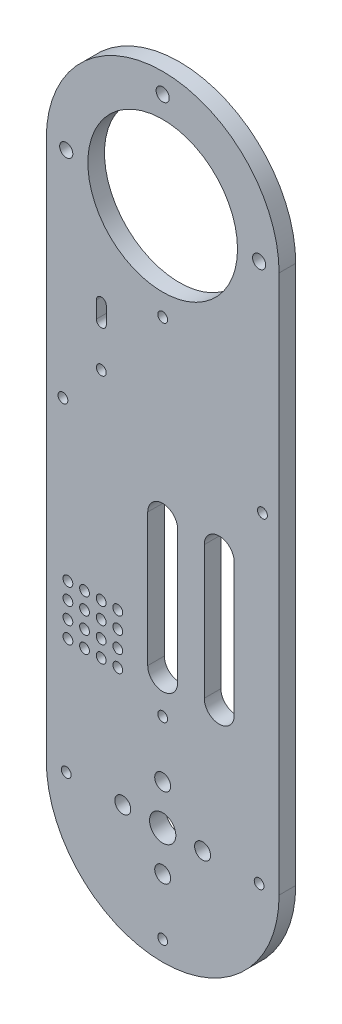
SolidWorks part; units mm, degrees
ref_plane "Front Plane" through (0, 0, 0) normal (0, 0, 1) x (1, 0, 0)
ref_plane "Top Plane" through (0, 0, 0) normal (0, 1, 0) x (1, 0, 0)
ref_plane "Right Plane" through (0, 0, 0) normal (1, 0, 0) x (0, 0, -1)
sketch "Sketch1" plane through (0, 0, 0) normal (0, 0, 1) x (1, 0, 0)
  line L0 (35, 0) -> (35, 162)
  line L1 (-35, 0) -> (-35, 162)
  line L2 (-35, 162) -> (35, 162) construction
  line L3 (0, 0) -> (35, 0) construction
  line L4 (0, 0) -> (0, 40) construction
  line L5 (0, 0) -> (25.0676, 25.0676) construction
  line L6 (0, 0) -> (0, 162) construction
  line L7 (0, 80) -> (0, 40) construction
  line L8 (4.5, 80) -> (4.5, 40)
  line L9 (-4.5, 80) -> (-4.5, 40)
  line L10 (0, 162) -> (0, 191) construction
  line L13 (17, 80) -> (17, 40) construction
  line L14 (21.5, 80) -> (21.5, 40)
  line L15 (12.5, 80) -> (12.5, 40)
  line L16 (-18.45, 127.5) -> (-18.45, 122.5) construction
  line L19 (-16.95, 127.5) -> (-16.95, 122.5)
  line L22 (-19.95, 127.5) -> (-19.95, 122.5)
  line L25 (-18.45, 110) -> (-18.45, 133.5287) construction
  line L28 (0, 162) -> (29, 162) construction
  line L29 (0, 162) -> (0, 133) construction
  line L30 (0, 162) -> (-29, 162) construction
  arc A0 (-35, 0) -> (35, 0) centre (0, 0) ccw
  arc A1 (35, 162) -> (-35, 162) centre (0, 162) ccw
  circle A2 centre (0, 0) radius 3.95
  arc A7 (4.5, 80) -> (-4.5, 80) centre (0, 80) ccw
  arc A8 (-4.5, 40) -> (4.5, 40) centre (0, 40) ccw
  circle A9 centre (0, 29) radius 1.475
  arc A12 (21.5, 80) -> (12.5, 80) centre (17, 80) ccw
  arc A13 (12.5, 40) -> (21.5, 40) centre (17, 40) ccw
  circle A22 centre (0, 162) radius 22.5
  circle A25 centre (0, 133) radius 1.475
  circle A26 centre (-30, 97) radius 1.475
  circle A27 centre (30, 97) radius 1.475
  arc A28 (-16.95, 127.5) -> (-19.95, 127.5) centre (-18.45, 127.5) ccw
  circle A29 centre (29, 0) radius 1.475
  circle A30 centre (0, -29) radius 1.475
  circle A31 centre (-29, 0) radius 1.475
  circle A32 centre (0, 12) radius 2.4
  circle A33 centre (12, 0) radius 2.4
  circle A34 centre (0, -12) radius 2.4
  circle A35 centre (-12, 0) radius 2.4
  circle A36 centre (0, 191) radius 1.975
  circle A37 centre (29, 162) radius 1.975
  circle A39 centre (-29, 162) radius 1.975
  circle A40 centre (0, 133) radius 1.975 [skipped]
  arc A41 (-19.95, 122.5) -> (-16.95, 122.5) centre (-18.45, 122.5) ccw
  circle A42 centre (-18.45, 110) radius 1.475
  circle A43 centre (-28.5, 35) radius 1.475
  circle A44 centre (-23.5, 35) radius 1.475
  circle A45 centre (-18.5, 35) radius 1.475
  circle A46 centre (-13.5, 35) radius 1.475
  circle A47 centre (-28.5, 40) radius 1.475
  circle A48 centre (-23.5, 40) radius 1.475
  circle A49 centre (-18.5, 40) radius 1.475
  circle A50 centre (-13.5, 40) radius 1.475
  circle A51 centre (-28.5, 45) radius 1.475
  circle A52 centre (-23.5, 45) radius 1.475
  circle A53 centre (-18.5, 45) radius 1.475
  circle A54 centre (-13.5, 45) radius 1.475
  circle A55 centre (-28.5, 50) radius 1.475
  circle A56 centre (-23.5, 50) radius 1.475
  circle A57 centre (-18.5, 50) radius 1.475
  circle A58 centre (-13.5, 50) radius 1.475
  point P13 (0, 60)
  point P21 (0, 0)
  point P28 (-18.45, 125)
  point P36 (17, 60)
  point P71 (0, 162)
  point P87 (0, 0)
  point P92 (0, 0)
  dimension "D1" = 70
  dimension "D4" = 7.9
  dimension "D6" = 4
  dimension "D11" = 4.5
  dimension "D12" = 2.95
  dimension "D16" = 29
  dimension "D18" = 4.5
  dimension "D22" = 1.5
  dimension "D24" = 16.55
  dimension "D27" = 45
  dimension "D28" = 2.95
  dimension "D30" = 2.95
  dimension "D32" = 2.95
  dimension "D7" = 4.8
  dimension "D15" = 3.95
  dimension "D23" = 2.95
  dimension "D2" = 162
  dimension "D3" = 162
  dimension "D5" = 45
  dimension "D9" = 40
  dimension "D10" = 40
  dimension "D13" = 29
  dimension "D14" = 13.5
  dimension "D17" = 4
  dimension "D19" = 40
  dimension "D20" = 60
  dimension "D21" = 5
  dimension "D25" = 52
  dimension "D26" = 12.5
  dimension "D29" = 6.5
  dimension "D31" = 29
  dimension "D33" = 65
  dimension "D34" = 5
  dimension "D8" = 12
  dimension "D36" = 35
  dimension "D37" = 4
  dimension "D38" = 4
  dimension "D35" = 4
extrude "Boss-Extrude1" add sketch "Sketch1" along normal blind 5
